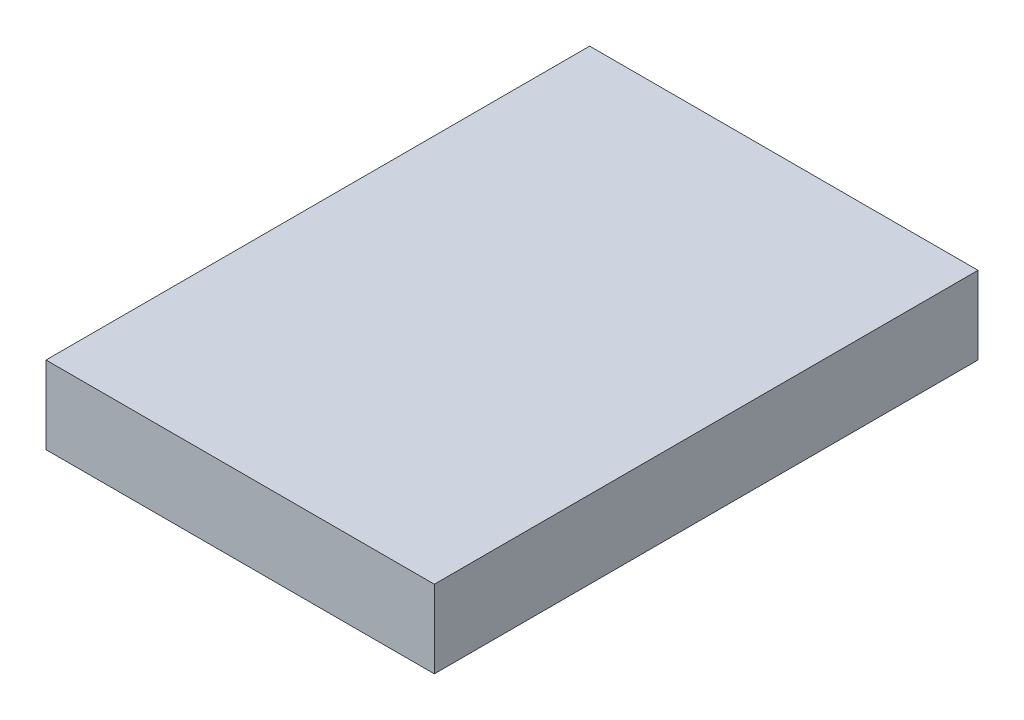
SolidWorks part; units mm, degrees
ref_plane "Front" through (0, 0, 0) normal (0, 0, 1) x (1, 0, 0)
ref_plane "Top" through (0, 0, 0) normal (0, 1, 0) x (1, 0, 0)
ref_plane "Right" through (0, 0, 0) normal (1, 0, 0) x (0, 0, -1)
sketch "Sketch1" plane through (0, 0, 0) normal (0, 1, 0) x (1, 0, 0)
  line L1 (-12.5, -17.5) -> (12.5, -17.5)
  line L2 (-12.5, -17.5) -> (-12.5, 17.5)
  line L3 (-12.5, 17.5) -> (12.5, 17.5)
  line L4 (12.5, -17.5) -> (12.5, 17.5)
  line L5 (-12.5, -17.5) -> (12.5, 17.5) construction
  line L6 (-12.5, 17.5) -> (12.5, -17.5) construction
  point P0 (0, 0)
  dimension "D1" = 25
  dimension "D2" = 35
extrude "Boss-Extrude1" add sketch "Sketch1" along normal blind 5
